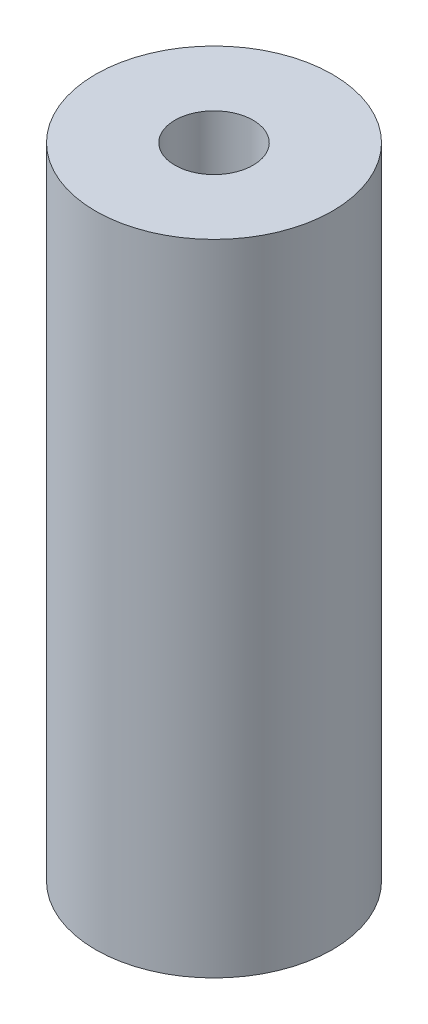
SolidWorks part; units mm, degrees
material "6061 Alloy"
ref_plane "Front Plane" through (0, 0, 0) normal (0, 0, 1) x (1, 0, 0)
ref_plane "Top Plane" through (0, 0, 0) normal (0, 1, 0) x (1, 0, 0)
ref_plane "Right Plane" through (0, 0, 0) normal (1, 0, 0) x (0, 0, -1)
sketch "Sketch1" plane through (0, 0, 0) normal (0, 1, 0) x (1, 0, 0)
  circle A0 centre (0, 0) radius 5
  dimension "D1" = 10
extrude "Boss-Extrude1" add sketch "Sketch1" along normal blind 27
hole_wizard "M4x0.7 Tapped Hole1" positions "Sketch2" profile "Sketch4" tap size "M4x0.7" standard "ANSI Metric" end condition through all
sketch "Sketch2" plane through (0, 27, 0) normal (0, 1, 0) x (1, 0, 0)
  point P0 (0, 0)
sketch "Sketch4" plane through (0, 27, 0) normal (1, 0, 0) x (0, 0, 1)
  line L0 (0, 0) -> (0, 27)
  line L1 (0, 27) -> (1.65, 27)
  line L2 (1.65, 27) -> (1.65, 0)
  line L5 (1.65, 0) -> (0, 0)
  line L11 (0, -6.35) -> (0, 107.95) construction
  dimension "Thru Tap Drill Dia." = 3.3
  dimension "Thru Tap Drill Depth" = 27
cosmetic thread "Hole Thread1" parameters "D2"=4
